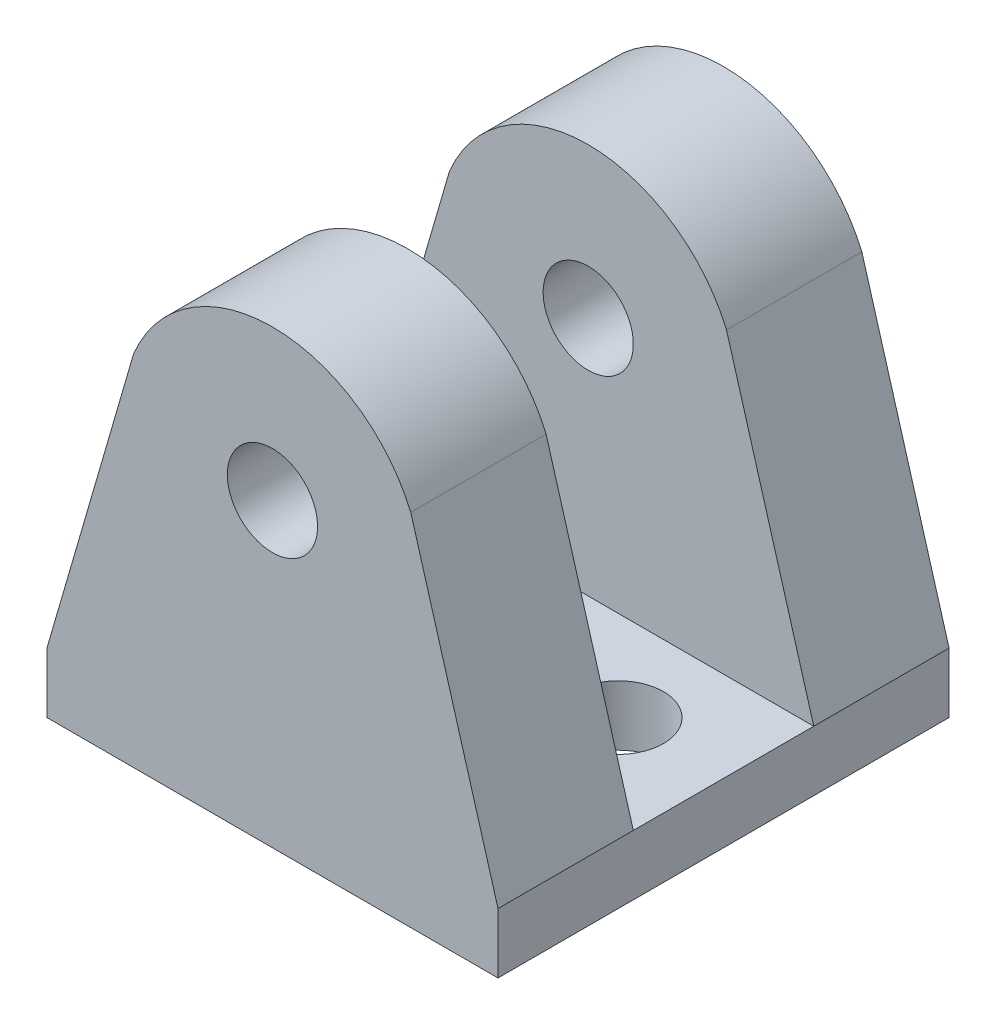
SolidWorks part; units mm, degrees
ref_plane "Front Plane" through (0, 0, 0) normal (0, 0, 1) x (1, 0, 0)
ref_plane "Top Plane" through (0, 0, 0) normal (0, 1, 0) x (1, 0, 0)
ref_plane "Right Plane" through (0, 0, 0) normal (1, 0, 0) x (0, 0, -1)
sketch "Sketch7" plane through (0, 0, 0) normal (0, 1, 0) x (1, 0, 0)
  line L0 (-7.5, 0) -> (7.5, 0)
  line L1 (7.5, 0) -> (7.5, -7.5)
  line L2 (7.5, -7.5) -> (-7.5, -7.5)
  line L3 (-7.5, -7.5) -> (-7.5, 0)
  point P4 (0, 0)
  dimension "D1" = 15
  dimension "D2" = 7.5
extrude "Boss-Extrude2" add sketch "Sketch7" along normal blind 2
sketch "Sketch8" plane through (0, 0, 0) normal (0, 0, -1) x (-1, 0, 0)
  line L0 (-4.599, 11.962) -> (-7.5, 2)
  line L1 (-7.5, 2) -> (7.5, 2) construction
  line L2 (4.615, 11.9239) -> (7.5, 2)
  line L3 (-7.5, 2) -> (7.5, 2)
  circle A0 centre (0, 10) radius 1.5
  arc A1 (-4.599, 11.962) -> (4.615, 11.9239) centre (0, 10) cw
extrude "Boss-Extrude3" add sketch "Sketch8" against normal blind 4.5
mirror "Mirror1" about plane through (7.5, 2, 7.5) normal (0, 0, -1) of "Boss-Extrude2", "Boss-Extrude3"
sketch "Sketch9" plane through (0, 2, 0) normal (0, 1, 0) x (1, 0, 0)
  circle A0 centre (4, -7.5) radius 1.5
extrude "Cut-Extrude1" cut sketch "Sketch9" against normal through all
mirror "Mirror2" about plane through (0, 0, 0) normal (1, 0, 0) of "Cut-Extrude1"
